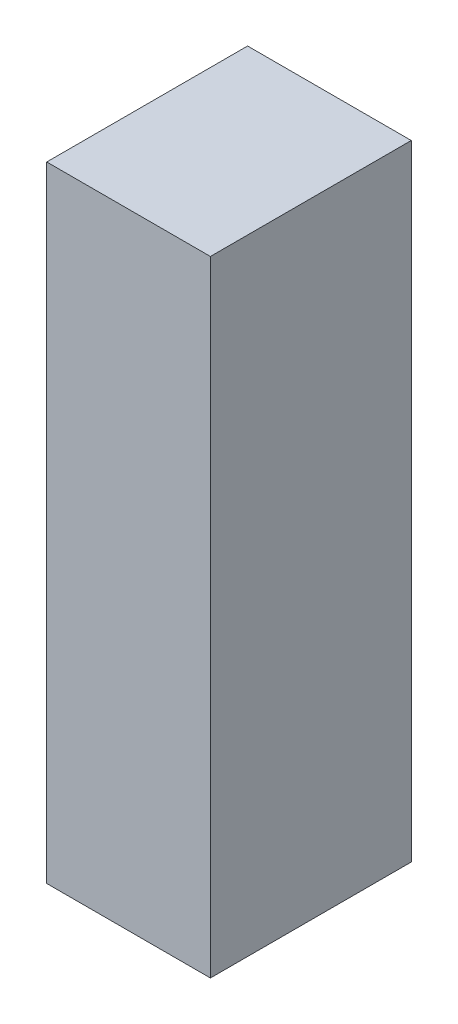
SolidWorks part; units mm, degrees
ref_plane "Front Plane" through (0, 0, 0) normal (0, 0, 1) x (1, 0, 0)
ref_plane "Top Plane" through (0, 0, 0) normal (0, 1, 0) x (1, 0, 0)
ref_plane "Right Plane" through (0, 0, 0) normal (1, 0, 0) x (0, 0, -1)
sketch "Sketch1" plane through (0, 0, 0) normal (0, 1, 0) x (1, 0, 0)
  line L1 (279.4, -342.9) -> (-279.4, -342.9)
  line L2 (279.4, -342.9) -> (279.4, 342.9)
  line L3 (279.4, 342.9) -> (-279.4, 342.9)
  line L4 (-279.4, -342.9) -> (-279.4, 342.9)
  line L5 (279.4, -342.9) -> (-279.4, 342.9) construction
  line L6 (279.4, 342.9) -> (-279.4, -342.9) construction
  point P0 (0, 0)
  dimension "D1" = 558.8
  dimension "D2" = 685.8
extrude "Boss-Extrude1" add sketch "Sketch1" along normal blind 2133.6
shell "Shell2" thickness 2.54
